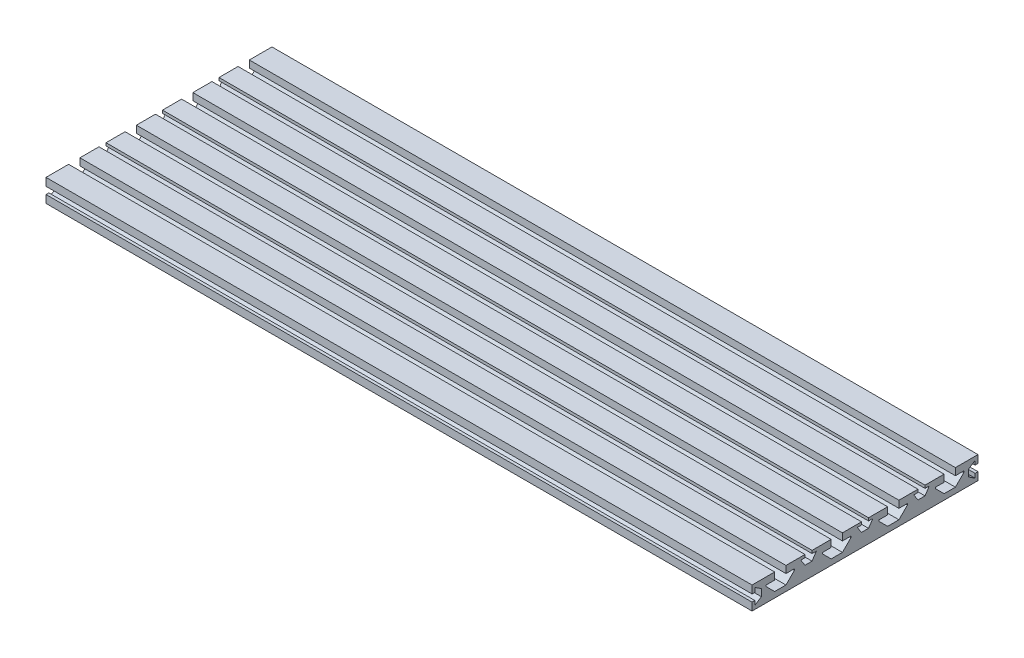
SolidWorks part; units mm, degrees
ref_plane "Front Plane" through (0, 0, 0) normal (0, 0, 1) x (1, 0, 0)
ref_plane "Top Plane" through (0, 0, 0) normal (0, 1, 0) x (1, 0, 0)
ref_plane "Right Plane" through (0, 0, 0) normal (1, 0, 0) x (0, 0, -1)
sketch "Sketch1" plane through (0, 0, 0) normal (1, 0, 0) x (0, 0, -1)
  line L0 (0, 59.2844) -> (0, -57.3499) construction
  line L1 (80, -7.2735) -> (-80, -7.2735)
  line L2 (2.5, 2.2265) -> (-2.5, 2.2265)
  line L3 (-2.5, 8.7265) -> (-16, 8.7265)
  line L4 (-80, -7.2735) -> (-80, -1.7735)
  line L5 (0, 0) -> (-80, 8.7265) construction
  line L6 (0, 0) -> (-80, -7.2735) construction
  line L7 (-2.5, 6.7265) -> (-2.5, 8.7265)
  line L8 (-2.5, 6.7265) -> (-5.5, 6.7265)
  line L9 (-5.5, 6.7265) -> (-2.5, 2.2265)
  line L10 (-24, 8.7265) -> (-37.5, 8.7265)
  line L11 (-80, 3.2265) -> (-80, 8.7265)
  line L12 (-30, 3.7265) -> (-30, 2.7265)
  line L13 (-24, -3.2735) -> (-16, -3.2735)
  line L14 (-10, 3.7265) -> (-10, 2.7265)
  line L15 (-30, 3.7265) -> (-24, 3.7265)
  line L16 (-64, 8.7265) -> (-80, 8.7265)
  line L17 (-42.5, 8.7265) -> (-56, 8.7265)
  line L18 (-24, 3.7265) -> (-24, 8.7265)
  line L19 (-10, 3.7265) -> (-16, 3.7265)
  line L20 (-45.5, 6.7265) -> (-42.5, 2.1227)
  line L21 (78, -1.7735) -> (78, 3.2265) construction
  line L22 (-16, 3.7265) -> (-16, 8.7265)
  line L23 (-37.5, 2.1227) -> (-42.5, 2.1227)
  line L24 (-42.5, 6.7265) -> (-45.5, 6.7265)
  line L25 (-42.5, 6.7265) -> (-42.5, 8.7265)
  line L26 (-40, 2.1227) -> (-40, 16.8363) construction
  line L27 (-37.5, 6.7265) -> (-37.5, 8.7265)
  line L28 (-37.5, 6.7265) -> (-34.5, 6.7265)
  line L29 (-34.5, 6.7265) -> (-37.5, 2.1227)
  line L30 (-70, 3.7265) -> (-64, 3.7265)
  line L31 (40, 2.1227) -> (40, 16.8363) construction
  line L32 (-56, 3.7265) -> (-56, 8.7265)
  line L33 (-50, 3.7265) -> (-50, 2.7265)
  line L34 (0, 0) -> (80, -7.2735) construction
  line L35 (0, 0) -> (80, 8.7265) construction
  line L36 (78, -1.7735) -> (80, -1.7735)
  line L37 (-70, 3.7265) -> (-70, 2.7265)
  line L38 (-64, -3.2735) -> (-56, -3.2735)
  line L39 (-64, 3.7265) -> (-64, 8.7265)
  line L40 (-50, 3.7265) -> (-56, 3.7265)
  line L41 (-73.3961, 3.2265) -> (-73.3961, -1.7735)
  line L42 (-78, 6.2265) -> (-73.3961, 3.2265)
  line L43 (-78, -1.7735) -> (-78, -4.7735)
  line L44 (-78, 3.2265) -> (-78, 6.2265)
  line L45 (-78, 3.2265) -> (-80, 3.2265)
  line L46 (-78, -4.7735) -> (-73.3961, -1.7735)
  line L47 (-78, -1.7735) -> (-80, -1.7735)
  line L48 (-78, -1.7735) -> (-78, 3.2265) construction
  line L49 (78, -4.7735) -> (73.3961, -1.7735)
  line L50 (78, 3.2265) -> (80, 3.2265)
  line L51 (78, 3.2265) -> (78, 6.2265)
  line L52 (78, -1.7735) -> (78, -4.7735)
  line L53 (78, 6.2265) -> (73.3961, 3.2265)
  line L54 (73.3961, 3.2265) -> (73.3961, -1.7735)
  line L55 (50, 3.7265) -> (56, 3.7265)
  line L56 (64, 3.7265) -> (64, 8.7265)
  line L57 (64, -3.2735) -> (56, -3.2735)
  line L58 (70, 3.7265) -> (70, 2.7265)
  line L59 (50, 3.7265) -> (50, 2.7265)
  line L60 (56, 3.7265) -> (56, 8.7265)
  line L61 (70, 3.7265) -> (64, 3.7265)
  line L62 (34.5, 6.7265) -> (37.5, 2.1227)
  line L63 (37.5, 6.7265) -> (34.5, 6.7265)
  line L64 (37.5, 6.7265) -> (37.5, 8.7265)
  line L65 (42.5, 6.7265) -> (42.5, 8.7265)
  line L66 (42.5, 6.7265) -> (45.5, 6.7265)
  line L67 (37.5, 2.1227) -> (42.5, 2.1227)
  line L68 (16, 3.7265) -> (16, 8.7265)
  line L69 (45.5, 6.7265) -> (42.5, 2.1227)
  line L70 (10, 3.7265) -> (16, 3.7265)
  line L71 (24, 3.7265) -> (24, 8.7265)
  line L72 (42.5, 8.7265) -> (56, 8.7265)
  line L73 (64, 8.7265) -> (80, 8.7265)
  line L74 (30, 3.7265) -> (24, 3.7265)
  line L75 (10, 3.7265) -> (10, 2.7265)
  line L76 (24, -3.2735) -> (16, -3.2735)
  line L77 (30, 3.7265) -> (30, 2.7265)
  line L78 (80, 3.2265) -> (80, 8.7265)
  line L79 (24, 8.7265) -> (37.5, 8.7265)
  line L80 (5.5, 6.7265) -> (2.5, 2.2265)
  line L81 (2.5, 6.7265) -> (5.5, 6.7265)
  line L82 (2.5, 6.7265) -> (2.5, 8.7265)
  line L83 (80, -7.2735) -> (80, -1.7735)
  line L84 (2.5, 8.7265) -> (16, 8.7265)
  line L85 (-70, 2.7265) -> (-64, -3.2735)
  line L86 (-50, 2.7265) -> (-56, -3.2735)
  line L87 (-30, 2.7265) -> (-24, -3.2735)
  line L88 (-16, -3.2735) -> (-10, 2.7265)
  line L89 (10, 2.7265) -> (16, -3.2735)
  line L90 (30, 2.7265) -> (24, -3.2735)
  line L91 (56, -3.2735) -> (50, 2.7265)
  line L92 (70, 2.7265) -> (64, -3.2735)
  point P0 (0, 0)
  point P2 (0, -7.2735)
  point P9 (78, 0.7265)
  point P14 (-10, -3.2735)
  point P15 (-30, -3.2735)
  point P34 (-50, -3.2735)
  point P35 (-70, -3.2735)
  point P43 (-78, 0.7265)
  point P64 (70, -3.2735)
  point P65 (50, -3.2735)
  point P82 (10, -3.2735)
  point P83 (30, -3.2735)
  point P88 (0, 2.2265)
  dimension "D1" = 80
  dimension "D2" = 16
  dimension "D3" = 6.5
  dimension "D4" = 2.5
  dimension "D5" = 3
  dimension "D6" = 12
  dimension "D7" = 20
  dimension "D8" = 10
  dimension "D9" = 8
  dimension "D10" = 5
  dimension "D11" = 2
  dimension "D12" = 8
extrude "Boss-Extrude1" add sketch "Sketch1" along normal blind 500
